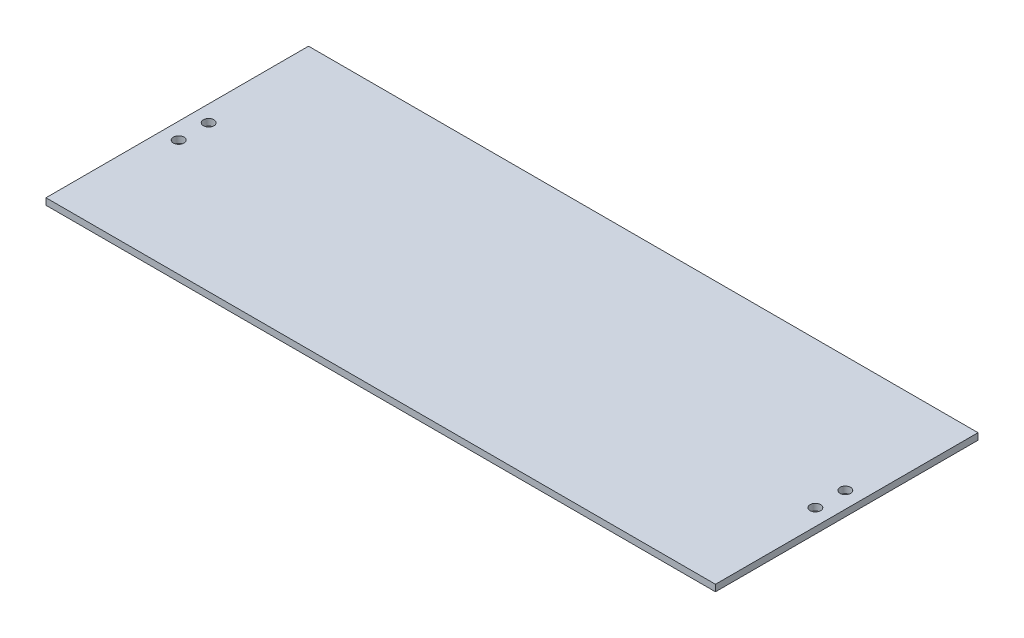
SolidWorks part; units mm, degrees
material "6061-T6 (SS)"
ref_plane "Front Plane" through (0, 0, 0) normal (0, 0, 1) x (1, 0, 0)
ref_plane "Top Plane" through (0, 0, 0) normal (0, 1, 0) x (1, 0, 0)
ref_plane "Right Plane" through (0, 0, 0) normal (1, 0, 0) x (0, 0, -1)
sketch "Sketch1" plane through (0, 0, 0) normal (0, 1, 0) x (1, 0, 0)
  line L1 (0, 0) -> (323.85, 0)
  line L2 (0, 0) -> (0, 127)
  line L3 (0, 127) -> (323.85, 127)
  line L4 (323.85, 0) -> (323.85, 127)
  dimension "D1" = 127
  dimension "D2" = 323.85
extrude "Boss-Extrude1" add sketch "Sketch1" along normal blind 3.175
hole_wizard "#10 Clearance Hole1" positions "Sketch3" profile "Sketch2" hole size "#10" standard "ANSI Inch"
sketch "Sketch3" plane through (0, 3.175, 0) normal (0, 1, 0) x (1, 0, 0)
  point P0 (315.9125, 70.75)
  point P3 (315.9125, 56.25)
  point P6 (7.9375, 70.75)
  point P9 (7.9375, 56.25)
sketch "Sketch2" plane through (315.9125, 3.175, -70.75) normal (1, 0, 0) x (0, 0, 1)
  line L0 (0, 0) -> (0, 14.2338)
  line L1 (0, 14.2338) -> (2.5527, 12.7)
  line L2 (2.5527, 12.7) -> (2.5527, 0)
  line L5 (2.5527, 0) -> (0, 0)
  line L10 (0, 14.2338) -> (-2.5527, 12.7) construction
  line L11 (0, -6.35) -> (0, 107.95) construction
  dimension "Hole Dia." = 5.1054
  dimension "Hole Depth" = 12.7
  dimension "Drill Angle" = 118
